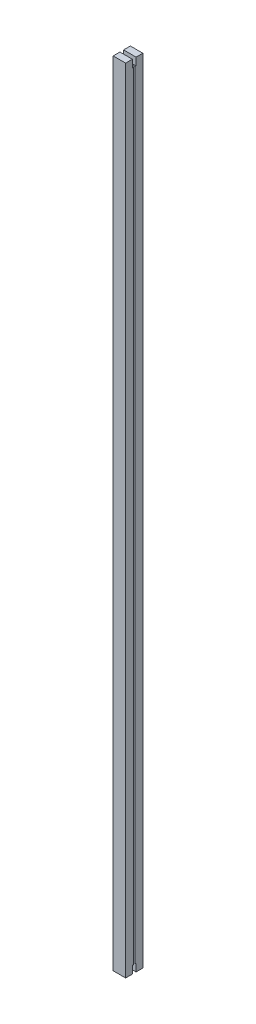
SolidWorks part; units mm, degrees
ref_plane "Спереди" through (0, 0, 0) normal (0, 0, 1) x (1, 0, 0)
ref_plane "Сверху" through (0, 0, 0) normal (0, 1, 0) x (1, 0, 0)
ref_plane "Справа" through (0, 0, 0) normal (1, 0, 0) x (0, 0, -1)
sketch "Эскиз1" plane through (0, 0, 0) normal (0, 1, 0) x (1, 0, 0)
  line L0 (-11.7649, 15) -> (10, 15)
  line L1 (10, 15) -> (10, 1.25)
  line L2 (10, 1.25) -> (6, 1.25)
  line L3 (6, 1.25) -> (6, -1.25)
  line L4 (-17.598, 0) -> (16.9433, 0) construction
  line L5 (-11.7649, 15) -> (-11.7649, -15)
  line L6 (10, -1.25) -> (6, -1.25)
  line L7 (10, -15) -> (10, -1.25)
  line L8 (-11.7649, -15) -> (10, -15)
  point P10 (-11.7649, 0)
  point P11 (6, 0)
  point P13 (0, 0)
  point P14 (0, 0)
  point P15 (0, 0)
  point P16 (0, 0)
extrude "Бобышка-Вытянуть1" add sketch "Эскиз1" along normal blind 1383.55
sketch "Эскиз2" plane through (-11.7649, 0, 0) normal (-1, 0, 0) x (0, 0, 1)
  line L0 (-3.1988, 0) -> (-3.1988, 13.2878)
  line L1 (-15, 0) -> (15, 0) construction
  line L2 (-3.1988, 13.2878) -> (3.1988, 13.2878)
  line L3 (-3.1988, 0) -> (3.1988, 0)
  line L4 (0, -13.6484) -> (0, 1403.8593) construction
  line L5 (3.1988, 0) -> (3.1988, 13.2878)
  line L6 (-108.4916, 691.775) -> (106.3349, 691.775) construction
  line L7 (3.1988, 1383.55) -> (3.1988, 1370.2622)
  line L8 (-3.1988, 1383.55) -> (3.1988, 1383.55)
  line L9 (-3.1988, 1370.2622) -> (3.1988, 1370.2622)
  line L10 (-3.1988, 1383.55) -> (-3.1988, 1370.2622)
  line L11 (15, 1383.55) -> (15, 0) construction
  point P10 (0, 0)
  point P11 (0, 13.2878)
  point P19 (15, 691.775)
extrude "Вырез-Вытянуть1" cut sketch "Эскиз2" against normal through all
